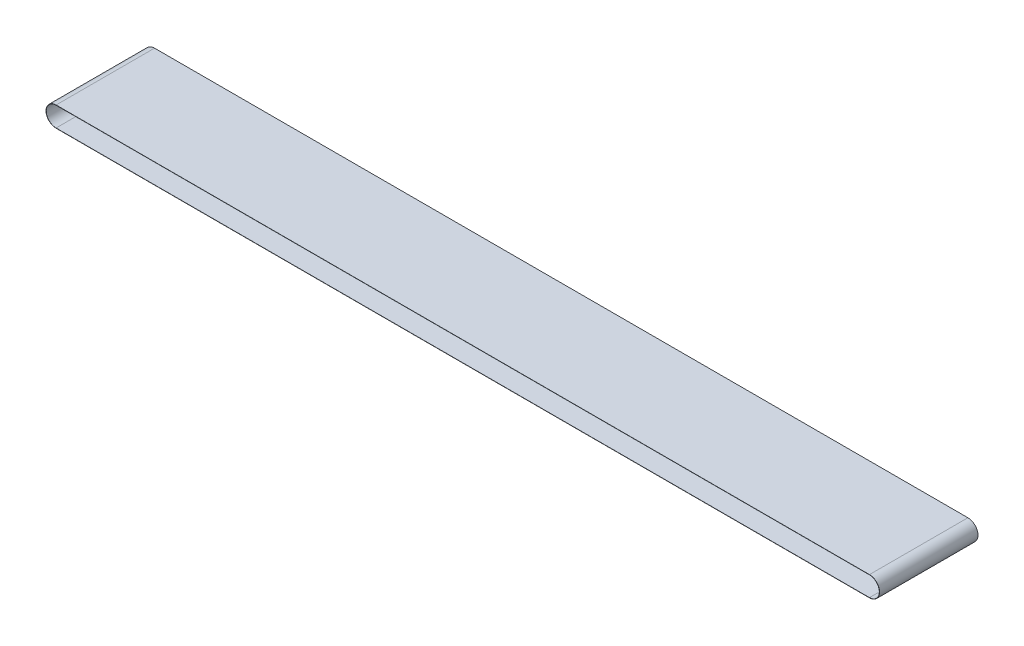
SolidWorks part; units mm, degrees
material "Rubber"
ref_plane "Front Plane" through (0, 0, 0) normal (0, 0, 1) x (1, 0, 0)
ref_plane "Top Plane" through (0, 0, 0) normal (0, 1, 0) x (1, 0, 0)
ref_plane "Right Plane" through (0, 0, 0) normal (1, 0, 0) x (0, 0, -1)
sketch "Sketch1" plane through (0, 0, 0) normal (0, 0, 1) x (1, 0, 0)
  line L0 (0, 0) -> (4130.96, 0) construction
  line L1 (0, 50) -> (4130.96, 50)
  line L2 (0, -50) -> (4130.96, -50)
  line L3 (0, -51.2) -> (4130.96, -51.2)
  line L4 (0, 51.2) -> (4130.96, 51.2)
  arc A0 (0, 50) -> (0, -50) centre (0, 0) ccw
  arc A1 (4130.96, -50) -> (4130.96, 50) centre (4130.96, 0) ccw
  arc A2 (0, 51.2) -> (0, -51.2) centre (0, 0) ccw
  arc A3 (4130.96, -51.2) -> (4130.96, 51.2) centre (4130.96, 0) ccw
  dimension "Overall_Length" = 4130.96
  dimension "D2" = 100
  dimension "D3" = 1.2
extrude "Boss-Extrude1" add sketch "Sketch1" along normal mid plane 500
